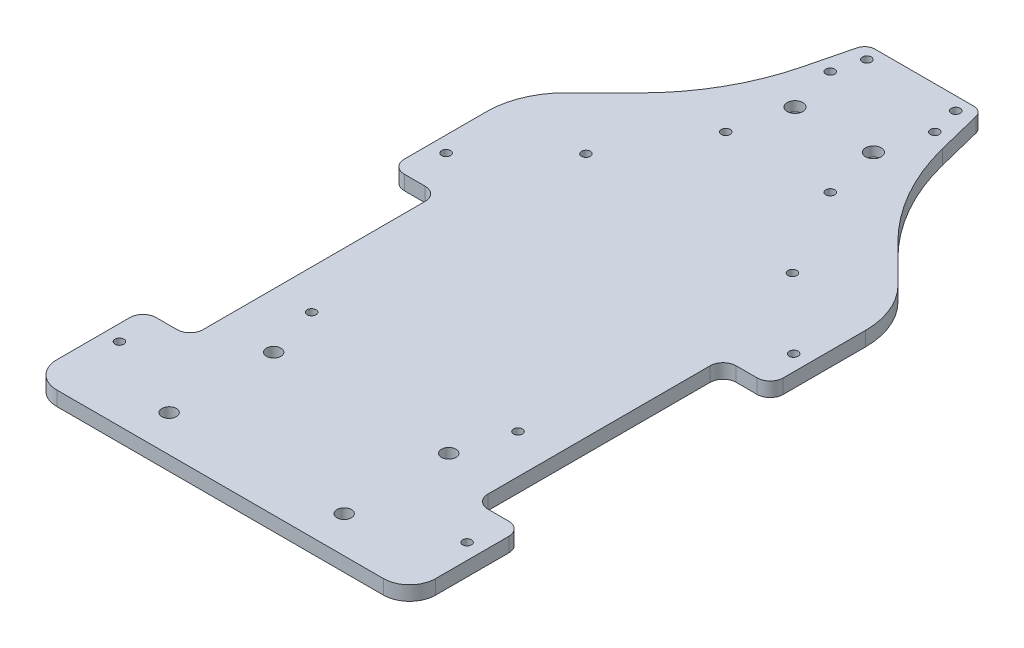
SolidWorks part; units mm, degrees
other "마크업1"
sketch "스케치14" plane through (72.5, 5.5, 213) normal (0.0297, 0.998, 0.056) x (0.9996, -0.0298, 0.0006)
ref_plane "정면" through (0, 0, 0) normal (0, 0, 1) x (1, 0, 0)
ref_plane "윗면" through (0, 0, 0) normal (0, 1, 0) x (1, 0, 0)
ref_plane "우측면" through (0, 0, 0) normal (1, 0, 0) x (0, 0, -1)
sketch "스케치1" plane through (0, 0, 0) normal (0, 1, 0) x (1, 0, 0)
  line L0 (-857.021, 0) -> (41994.0268, 0) construction
  line L1 (0, -857.021) -> (0, 41994.0268) construction
  line L2 (-72.5, 0) -> (-72.5, -180)
  line L3 (-72.5, 95) -> (72.5, 95) construction
  line L4 (-72.5, 95) -> (-72.5, -190) construction
  line L5 (-72.5, -190) -> (-47.5, -190) construction
  line L6 (72.5, 95) -> (72.5, -190) construction
  line L7 (-62.5, -190) -> (-49.1961, -190)
  line L8 (72.5, -180) -> (72.5, 0)
  line L9 (-15.8039, -213) -> (15.8039, -213)
  line L14 (-18.846, -211.968) -> (-46.154, -191.032)
  line L15 (-22, 95) -> (22, 95)
  line L16 (-63.6708, 21.2555) -> (-49.4782, 35.3915)
  line L17 (18.846, -211.968) -> (46.154, -191.032)
  line L18 (857.021, 0) -> (-41994.0268, 0) construction
  line L23 (47.5, -190) -> (72.5, -190) construction
  line L24 (49.1961, -190) -> (62.5, -190)
  line L25 (-27, 75) -> (-22, 95)
  line L26 (63.6708, 21.2555) -> (49.4782, 35.3915)
  line L27 (27, 75) -> (22, 95)
  arc A4 (62.5, -190) -> (72.5, -180) centre (62.5, -180) ccw
  arc A5 (-62.5, -190) -> (-72.5, -180) centre (-62.5, -180) cw
  arc A12 (49.1961, -190) -> (46.154, -191.032) centre (49.1961, -195) ccw
  arc A13 (18.846, -211.968) -> (15.8039, -213) centre (15.8039, -208) cw
  arc A14 (-15.8039, -213) -> (-18.846, -211.968) centre (-15.8039, -208) cw
  arc A15 (-49.1961, -190) -> (-46.154, -191.032) centre (-49.1961, -195) cw
  arc A16 (-72.5, 0) -> (-63.6708, 21.2555) centre (-42.5, 0) cw
  arc A17 (-49.4782, 35.3915) -> (-27, 75) centre (-109.4621, 95.6155) ccw
  arc A18 (72.5, 0) -> (63.6708, 21.2555) centre (42.5, 0) ccw
  arc A19 (49.4782, 35.3915) -> (27, 75) centre (109.4621, 95.6155) cw
  point P4 (0, 0)
  point P36 (0, -213)
  point P40 (0, 95)
  point P77 (17.5, -213)
  point P80 (-17.5, -213)
  dimension "D8" = 10
  dimension "D13" = 72.5
  dimension "D14" = 5
  dimension "D17" = 20
  dimension "D15" = 30
  dimension "D16" = 85
  dimension "D1" = 145
  dimension "D2" = 285
  dimension "D3" = 190
  dimension "D9" = 35
  dimension "D10" = 23
  dimension "D11" = 25
  dimension "D12" = 44
  dimension "D18" = 5
extrude "Deck base" add sketch "스케치1" along normal blind 5.5 contours L2 A5 L7 A15 L14 A14 L9 A13 L17 A12 L24 A4 L8 A18 L26 A19 L27 L15 L25 A17 L16 A16
sketch "스케치3" plane through (0, 5.5, 0) normal (0, 1, 0) x (1, 0, 0)
  line L0 (-22, 95) -> (22, 95) construction
  line L2 (72.5, -180) -> (72.5, 0) construction
  line L3 (66.5, -146.5) -> (66.5, 0) construction
  line L4 (-200857.021, 0) -> (241994.0268, 0) construction
  line L5 (0, -3.025) -> (0, 3.025) construction
  line L6 (0, -200857.021) -> (0, 241994.0268) construction
  circle A0 centre (17, 90) radius 1.7
  circle A1 centre (66.5, -146.5) radius 1.7
  circle A2 centre (66.5, -116.5) radius 1.7
  circle A3 centre (66.5, -51.5) radius 1.7
  circle A4 centre (66.5, -21.5) radius 1.7
  circle A5 centre (-66.5, -21.5) radius 1.7
  circle A6 centre (-66.5, -51.5) radius 1.7
  circle A7 centre (-66.5, -116.5) radius 1.7
  circle A8 centre (-66.5, -146.5) radius 1.7
  circle A9 centre (-17, 90) radius 1.7
  dimension "D1" = 3.4
  dimension "D3" = 3.4
  dimension "D6" = 3.4
  dimension "D8" = 3.4
  dimension "D9" = 3.4
  dimension "D2" = 5
  dimension "D4" = 111.5
  dimension "D5" = 6
  dimension "D7" = 30
  dimension "D10" = 65
  dimension "D11" = 30
  dimension "D12" = 17
extrude "Bolt slot" cut sketch "스케치3" against normal up to next
fillet "필렛1" radius 4 2 edges at (22, 2.75, -95) (-22, 2.75, -95)
sketch "스케치11" plane through (0, 5.5, 0) normal (0, 1, 0) x (1, 0, 0)
  line L0 (-72.5, 0) -> (-72.5, -180) construction
  line L1 (-72.5, -36.5) -> (-54.5, -36.5)
  line L2 (-72.5, -36.5) -> (-72.5, -131.5)
  line L3 (-72.5, -131.5) -> (-54.5, -131.5)
  line L4 (-54.5, -36.5) -> (-54.5, -131.5)
  line L5 (0, 95) -> (0, -174.2944) construction
  line L6 (-22, 95) -> (22, 95) construction
  line L7 (0, -200857.021) -> (0, 241994.0268) construction
  line L8 (72.5, -131.5) -> (54.5, -131.5)
  line L9 (54.5, -36.5) -> (54.5, -131.5)
  line L10 (72.5, -36.5) -> (54.5, -36.5)
  line L11 (72.5, -36.5) -> (72.5, -131.5)
  circle A0 centre (-66.5, -21.5) radius 1.7 construction
  circle A1 centre (-66.5, -146.5) radius 1.7 construction
  dimension "D2" = 15
  dimension "D3" = 15
  dimension "D1" = 18
extrude "Cut side" cut sketch "스케치11" against normal up to next
sketch "스케치10" plane through (0, 5.5, 0) normal (0, 1, 0) x (1, 0, 0)
  line L0 (-72.5, 0) -> (-72.5, -180) construction
  line L1 (-72.5, -174.5) -> (72.5, -174.5)
  line L2 (-72.5, -174.5) -> (-72.5, -213)
  line L3 (-72.5, -213) -> (72.5, -213)
  line L4 (72.5, -174.5) -> (72.5, -213)
  line L5 (72.5, -180) -> (72.5, 0) construction
  line L6 (-15.8039, -213) -> (15.8039, -213) construction
  circle A0 centre (-66.5, -146.5) radius 1.7 construction
  dimension "D1" = 28
extrude "Cut tail" cut sketch "스케치10" against normal up to next
fillet "필렛2" radius 10 2 edges at (72.5, 2.75, 174.5) (-72.5, 2.75, 174.5)
fillet "필렛3" radius 5 8 edges at (54.5, 2.75, 36.5) (72.5, 2.75, 36.5) (54.5, 2.75, 131.5) (72.5, 2.75, 131.5) (-54.5, 2.75, 131.5) (-72.5, 2.75, 131.5) (-54.5, 2.75, 36.5) (-72.5, 2.75, 36.5)
sketch "스케치4" plane through (0, 5.5, 0) normal (0, 1, 0) x (1, 0, 0)
  line L0 (-22, 95) -> (22, 95) construction
  line L1 (-20, 79) -> (20, 79) construction
  line L2 (-20, 79) -> (-20, 39) construction
  line L3 (-20, 39) -> (20, 39) construction
  line L4 (20, 79) -> (20, 39) construction
  line L5 (0, -200857.021) -> (0, 241994.0268) construction
  line L6 (0, -3.025) -> (0, 3.025) construction
  circle A0 centre (-20, 79) radius 1.7
  circle A1 centre (-20, 39) radius 1.7
  circle A2 centre (20, 39) radius 1.7
  circle A3 centre (20, 79) radius 1.7
  point P6 (0, 79)
  dimension "D4" = 3.4
  dimension "D5" = 3.4
  dimension "D1" = 40
  dimension "D2" = 40
  dimension "D3" = 16
extrude "Lidar slot" cut sketch "스케치4" against normal up to next
sketch "스케치9" plane through (0, 5.5, 0) normal (0, 1, 0) x (1, 0, 0)
  line L0 (0, -200857.021) -> (0, 241994.0268) construction
  line L1 (-24.5, 84) -> (24.5, 84) construction
  line L2 (-24.5, 84) -> (-24.5, 34) construction
  line L3 (-24.5, 34) -> (-12.5, 34) construction
  line L4 (24.5, 84) -> (24.5, 34) construction
  line L5 (-24.5, 84) -> (24.5, 34) construction
  line L6 (-24.5, 34) -> (24.5, 84) construction
  line L7 (-12.5, 29) -> (12.5, 29) construction
  line L8 (-20, 79) -> (20, 79) construction
  line L9 (12.5, 29) -> (12.5, 34) construction
  line L10 (-12.5, 29) -> (-12.5, 34) construction
  line L11 (12.5, 34) -> (24.5, 34) construction
  point P0 (0, 59)
  point P11 (0, 29)
  dimension "D1" = 49
  dimension "D2" = 50
  dimension "D3" = 5
  dimension "D4" = 25
  dimension "D5" = 5
sketch "스케치6" plane through (0, 5.5, 0) normal (0, 1, 0) x (1, 0, 0)
  line L0 (0, -200857.021) -> (0, 241994.0268) construction
  line L1 (-37, -104.5) -> (37, -104.5) construction
  line L2 (-37, -104.5) -> (-37, -174.5) construction
  line L3 (-37, -174.5) -> (37, -174.5) construction
  line L4 (37, -104.5) -> (37, -174.5) construction
  line L6 (0, -3.025) -> (0, 3.025) construction
  line L7 (-12.5, 29) -> (12.5, 29) construction
  circle A0 centre (33.5, -120.5) radius 2.75
  circle A1 centre (33.5, -160.5) radius 2.75
  circle A2 centre (-33.5, -160.5) radius 2.75
  circle A3 centre (-33.5, -120.5) radius 2.75
  point P4 (0, -104.5)
  dimension "D3" = 5.5
  dimension "D6" = 5.5
  dimension "D1" = 74
  dimension "D2" = 70
  dimension "D4" = 16
  dimension "D5" = 3.5
  dimension "D7" = 3.5
  dimension "D8" = 14
  dimension "D9" = 133.5
extrude "Vesc slot" cut sketch "스케치6" against normal up to next
sketch "스케치7" plane through (0, 5.5, 0) normal (0, 1, 0) x (1, 0, 0)
  line L0 (0, -200857.021) -> (0, 241994.0268) construction
  line L1 (-43.5, 9) -> (43.5, 9) construction
  line L2 (-43.5, 9) -> (-43.5, -104) construction
  line L3 (-43.5, -104) -> (43.5, -104) construction
  line L4 (43.5, 9) -> (43.5, -104) construction
  line L7 (12.5, 34) -> (24.5, 34) construction
  circle A0 centre (39.5, 5) radius 1.7
  circle A1 centre (39.5, -100) radius 1.7
  circle A2 centre (-39.5, -100) radius 1.7
  circle A3 centre (-39.5, 5) radius 1.7
  point P4 (0, 9)
  dimension "D6" = 3.4
  dimension "D9" = 3.4
  dimension "D10" = 3.4
  dimension "D13" = 3.4
  dimension "D1" = 113
  dimension "D2" = 87
  dimension "D3" = 25
  dimension "D4" = 4
  dimension "D5" = 4
  dimension "D7" = 4
  dimension "D8" = 4
  dimension "D11" = 4
  dimension "D12" = 4
extrude "Nano slot" cut sketch "스케치7" against normal up to next
sketch "스케치12" plane through (0, 5.5, 0) normal (0, 1, 0) x (1, 0, 0)
  line L0 (-24.5, 34) -> (24.5, 84) construction
  line L1 (-12, 75.5) -> (12, 75.5) construction
  line L2 (-12, 75.5) -> (-12, 42.5) construction
  line L3 (-12, 42.5) -> (12, 42.5) construction
  line L4 (12, 75.5) -> (12, 42.5) construction
  line L5 (-12, 75.5) -> (12, 42.5) construction
  line L6 (-12, 42.5) -> (12, 75.5) construction
  circle A0 centre (-15, 60.5) radius 1.75
  circle A1 centre (15, 60.5) radius 1.75
  point P0 (0, 59)
  dimension "D3" = 3.5
  dimension "D4" = 3.5
  dimension "D1" = 24
  dimension "D2" = 33
  dimension "D5" = 15
  dimension "D6" = 15
  dimension "D7" = 15
extrude "컷-돌출3" cut sketch "스케치12" against normal up to next
sketch "스케치13" plane through (0, 5.5, 0) normal (0, 1, 0) x (1, 0, 0)
  circle A0 centre (-15, 60.5) radius 3
  circle A1 centre (15, 60.5) radius 3
  dimension "D1" = 6
  dimension "D2" = 6
extrude "컷-돌출4" cut sketch "스케치13" against normal blind 3.7
